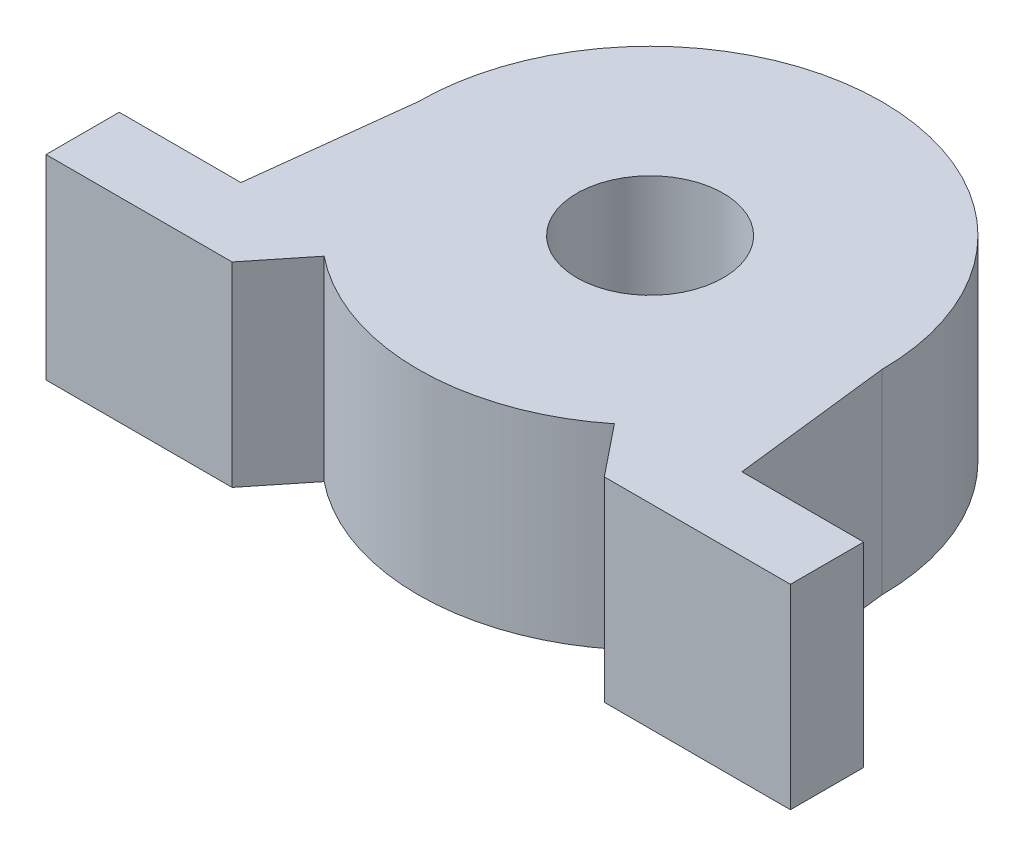
SolidWorks part; units mm, degrees
ref_plane "Front Plane" through (0, 0, 0) normal (0, 0, 1) x (1, 0, 0)
ref_plane "Top Plane" through (0, 0, 0) normal (0, 1, 0) x (1, 0, 0)
ref_plane "Right Plane" through (0, 0, 0) normal (1, 0, 0) x (0, 0, -1)
sketch "Sketch2" plane through (0, 0, 0) normal (0, 1, 0) x (1, 0, 0)
  line L0 (-15.25, -19) -> (-30.5, -19)
  line L1 (-30.5, -19) -> (-30.5, -13)
  line L2 (-30.5, -13) -> (-20.5243, -13)
  line L3 (-20.5243, -13) -> (-19, 0)
  line L4 (-15.25, -19) -> (-11.893, -14.8175)
  line L5 (0, 19) -> (0, -19) construction
  line L6 (20.5243, -13) -> (19, 0)
  line L7 (15.25, -19) -> (11.893, -14.8175)
  line L8 (30.5, -13) -> (20.5243, -13)
  line L9 (30.5, -19) -> (30.5, -13)
  line L10 (15.25, -19) -> (30.5, -19)
  circle A0 centre (0, 0) radius 6
  arc A1 (-11.893, -14.8175) -> (11.893, -14.8175) centre (0, 0) ccw
  arc A2 (19, 0) -> (-19, 0) centre (0, 0) ccw
  dimension "D1" = 12
  dimension "D2" = 38
  dimension "D4" = 6
extrude "Boss-Extrude2" add sketch "Sketch2" along normal blind 16
